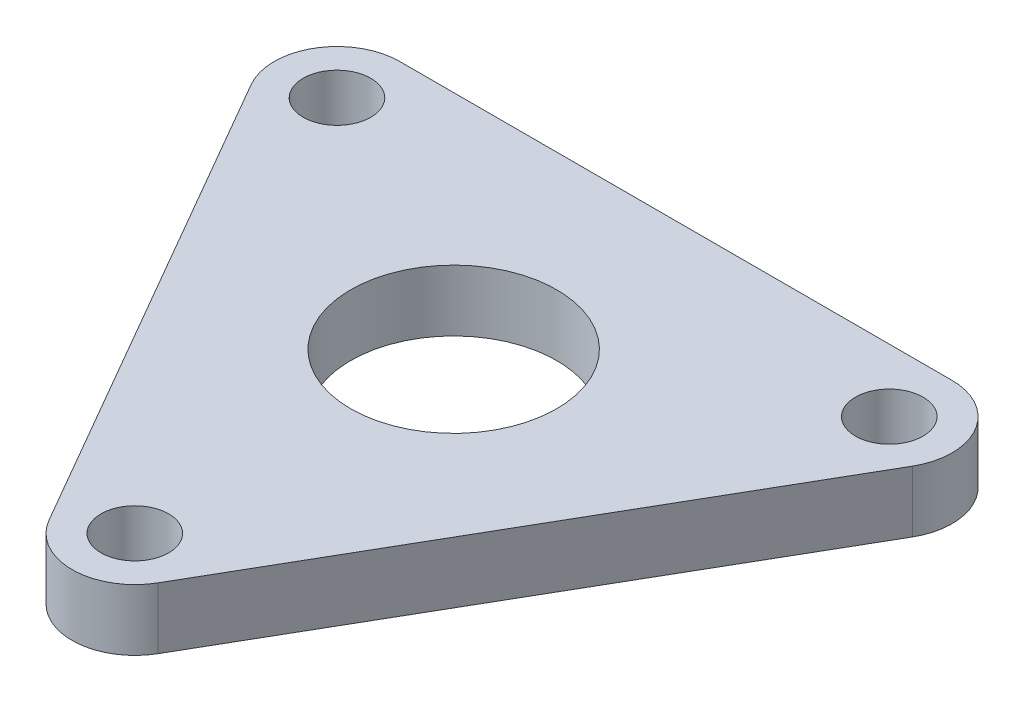
SolidWorks part; units mm, degrees
material "1023 Carbon Steel Sheet (SS)"
ref_plane "Front Plane" through (0, 0, 0) normal (0, 0, 1) x (1, 0, 0)
ref_plane "Top Plane" through (0, 0, 0) normal (0, 1, 0) x (1, 0, 0)
ref_plane "Right Plane" through (0, 0, 0) normal (1, 0, 0) x (0, 0, -1)
sketch "Sketch1" plane through (0, 0, 0) normal (0, 1, 0) x (1, 0, 0)
  line L0 (0, 16.5) -> (-14.2894, 8.25) construction
  line L1 (-14.2894, 8.25) -> (-14.2894, -8.25) construction
  line L2 (-17.104, 6.625) -> (-2.8146, -18.125)
  line L3 (2.8146, -18.125) -> (17.104, 6.625)
  line L4 (-14.2894, 11.5) -> (14.2894, 11.5)
  circle A0 centre (0, 0) radius 19.75 construction
  circle A1 centre (0, 0) radius 16.5 construction
  circle A2 centre (0, 0) radius 5.334
  circle A3 centre (0, 16.5) radius 1.75 construction
  circle A4 centre (-14.2894, 8.25) radius 1.75
  circle A5 centre (-14.2894, -8.25) radius 1.75 construction
  circle A6 centre (0, -16.5) radius 1.75
  circle A7 centre (14.2894, -8.25) radius 1.75 construction
  circle A8 centre (14.2894, 8.25) radius 1.75
  arc A9 (-14.2894, 11.5) -> (-17.104, 6.625) centre (-14.2894, 8.25) ccw
  arc A10 (17.104, 6.625) -> (14.2894, 11.5) centre (14.2894, 8.25) ccw
  arc A11 (-2.8146, -18.125) -> (2.8146, -18.125) centre (0, -16.5) ccw
  dimension "D1" = 39.5
  dimension "D2" = 33
  dimension "D3" = 10.668
  dimension "D4" = 3.5
extrude "Boss-Extrude1" add sketch "Sketch1" along normal blind 3.175
